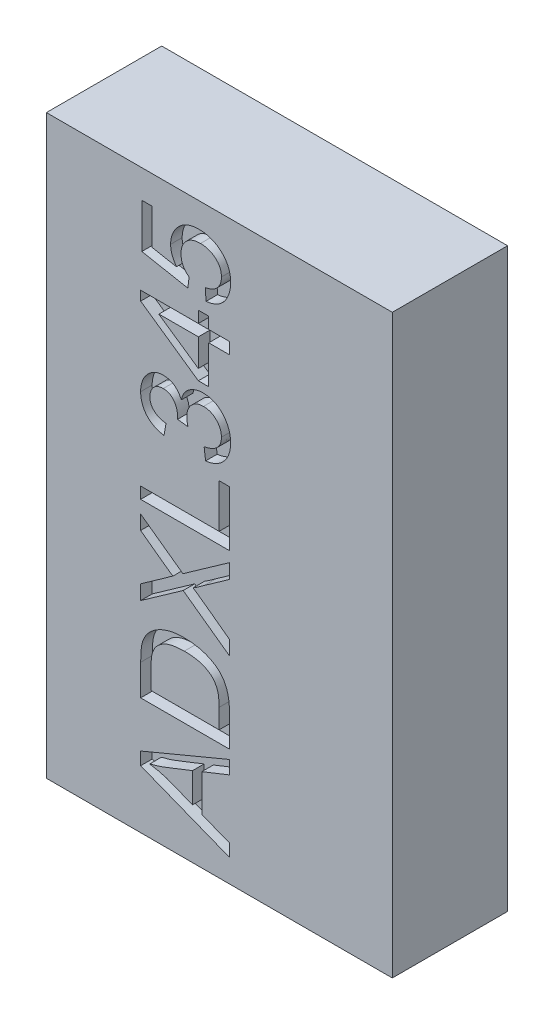
SolidWorks part; units mm, degrees
material "Plastique personnalisé"
ref_plane "Plan de face" through (0, 0, 0) normal (0, 0, 1) x (1, 0, 0)
ref_plane "Plan de dessus" through (0, 0, 0) normal (0, 1, 0) x (1, 0, 0)
ref_plane "Plan de droite" through (0, 0, 0) normal (1, 0, 0) x (0, 0, -1)
sketch "Esquisse1" plane through (0, 0, 0) normal (0, 0, 1) x (1, 0, 0)
  line L1 (0, 0) -> (3, 0)
  line L2 (0, 0) -> (0, 5)
  line L3 (0, 5) -> (3, 5)
  line L4 (3, 0) -> (3, 5)
  dimension "D1" = 3
  dimension "D2" = 5
extrude "Boss.-Extru.1" add sketch "Esquisse1" along normal blind 1
sketch "Esquisse2" plane through (3.5756, -1.2802, 1) normal (0, 0, 1) x (0, 1, 0)
  text T0 "ADXL345" font "@Arial Unicode MS" height in points 3
extrude "Enlèv. mat.-Extru.1" cut sketch "Esquisse2" against normal blind 0.1
